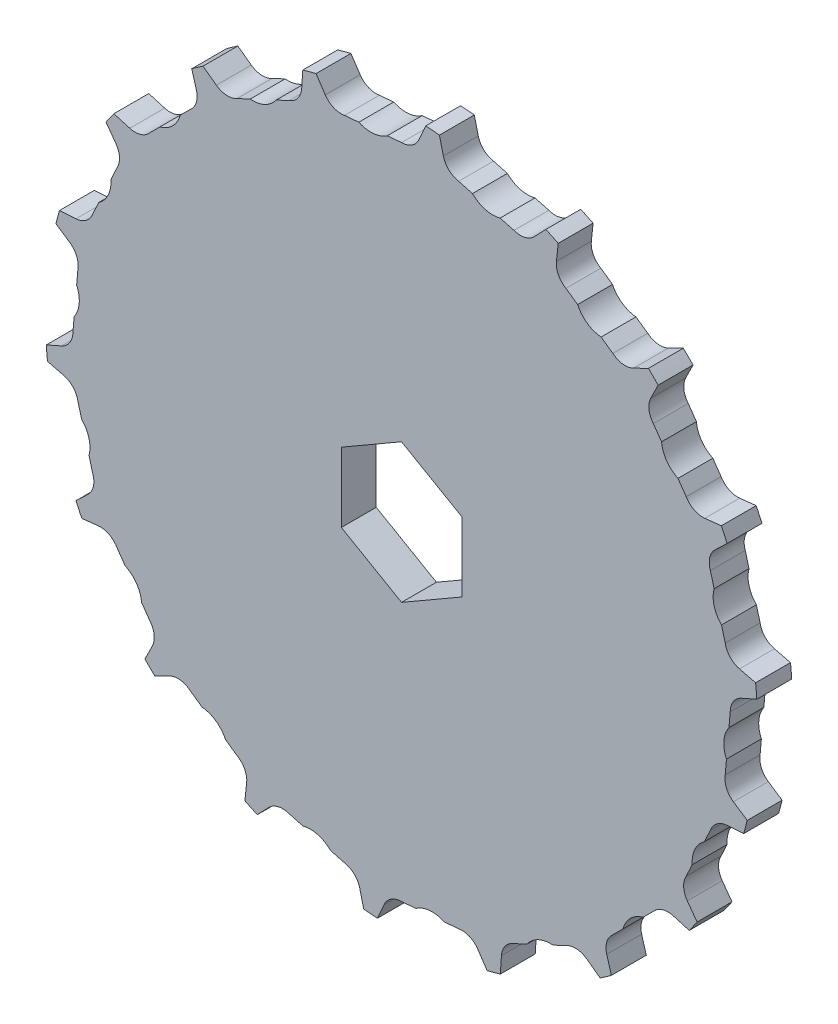
SolidWorks part; units mm, degrees
ref_plane "Front Plane" through (0, 0, 0) normal (0, 0, 1) x (1, 0, 0)
ref_plane "Top Plane" through (0, 0, 0) normal (0, 1, 0) x (1, 0, 0)
ref_plane "Right Plane" through (0, 0, 0) normal (1, 0, 0) x (0, 0, -1)
sketch "Sketch1" plane through (0, 0, 0) normal (0, 0, 1) x (1, 0, 0)
  line L0 (3.6596, 71.1503) -> (5.6741, 75.716)
  line L1 (3.6596, 71.1503) -> (8.7511, 70.7049) construction
  line L2 (7.5601, 75.551) -> (8.7511, 70.7049)
  line L3 (3.6596, 71.1503) -> (0, 0) construction
  line L4 (0, 0) -> (8.7511, 70.7049) construction
  line L5 (15.9591, 69.4339) -> (18.7358, 73.5804)
  line L6 (20.5645, 73.0904) -> (20.8959, 68.1111)
  line L7 (27.7738, 65.6078) -> (31.2283, 69.2091)
  line L8 (32.9441, 68.409) -> (32.4058, 63.4478)
  line L9 (38.7445, 59.7882) -> (42.7719, 62.7349)
  line L10 (44.3227, 61.649) -> (42.9311, 56.8567)
  line L11 (48.538, 52.1519) -> (53.0159, 54.3546)
  line L12 (54.3546, 53.0159) -> (52.1519, 48.538)
  line L13 (56.8567, 42.9311) -> (61.649, 44.3227)
  line L14 (62.7349, 42.7719) -> (59.7882, 38.7445)
  line L15 (63.4478, 32.4058) -> (68.409, 32.9441)
  line L16 (69.2091, 31.2283) -> (65.6078, 27.7738)
  line L17 (68.1111, 20.8959) -> (73.0904, 20.5645)
  line L18 (73.5804, 18.7358) -> (69.4339, 15.9591)
  line L19 (70.7049, 8.7511) -> (75.551, 7.5601)
  line L20 (75.716, 5.6741) -> (71.1503, 3.6596)
  line L21 (71.1503, -3.6596) -> (75.716, -5.6741)
  line L22 (75.551, -7.5601) -> (70.7049, -8.7511)
  line L23 (69.4339, -15.9591) -> (73.5804, -18.7358)
  line L24 (73.0904, -20.5645) -> (68.1111, -20.8959)
  line L25 (65.6078, -27.7738) -> (69.2091, -31.2283)
  line L26 (68.409, -32.9441) -> (63.4478, -32.4058)
  line L27 (59.7882, -38.7445) -> (62.7349, -42.7719)
  line L28 (61.649, -44.3227) -> (56.8567, -42.9311)
  line L29 (52.1519, -48.538) -> (54.3546, -53.0159)
  line L30 (53.0159, -54.3546) -> (48.538, -52.1519)
  line L31 (42.9311, -56.8567) -> (44.3227, -61.649)
  line L32 (42.7719, -62.7349) -> (38.7445, -59.7882)
  line L33 (32.4058, -63.4478) -> (32.9441, -68.409)
  line L34 (31.2283, -69.2091) -> (27.7738, -65.6078)
  line L35 (20.8959, -68.1111) -> (20.5645, -73.0904)
  line L36 (18.7358, -73.5804) -> (15.9591, -69.4339)
  line L37 (8.7511, -70.7049) -> (7.5601, -75.551)
  line L38 (5.6741, -75.716) -> (3.6596, -71.1503)
  line L39 (-3.6596, -71.1503) -> (-5.6741, -75.716)
  line L40 (-7.5601, -75.551) -> (-8.7511, -70.7049)
  line L41 (-15.9591, -69.4339) -> (-18.7358, -73.5804)
  line L42 (-20.5645, -73.0904) -> (-20.8959, -68.1111)
  line L43 (-27.7738, -65.6078) -> (-31.2283, -69.2091)
  line L44 (-32.9441, -68.409) -> (-32.4058, -63.4478)
  line L45 (-38.7445, -59.7882) -> (-42.7719, -62.7349)
  line L46 (-44.3227, -61.649) -> (-42.9311, -56.8567)
  line L47 (-48.538, -52.1519) -> (-53.0159, -54.3546)
  line L48 (-54.3546, -53.0159) -> (-52.1519, -48.538)
  line L49 (-56.8567, -42.9311) -> (-61.649, -44.3227)
  line L50 (-62.7349, -42.7719) -> (-59.7882, -38.7445)
  line L51 (-63.4478, -32.4058) -> (-68.409, -32.9441)
  line L52 (-69.2091, -31.2283) -> (-65.6078, -27.7738)
  line L53 (-68.1111, -20.8959) -> (-73.0904, -20.5645)
  line L54 (-73.5804, -18.7358) -> (-69.4339, -15.9591)
  line L55 (-70.7049, -8.7511) -> (-75.551, -7.5601)
  line L56 (-75.716, -5.6741) -> (-71.1503, -3.6596)
  line L57 (-71.1503, 3.6596) -> (-75.716, 5.6741)
  line L58 (-75.551, 7.5601) -> (-70.7049, 8.7511)
  line L59 (-69.4339, 15.9591) -> (-73.5804, 18.7358)
  line L60 (-73.0904, 20.5645) -> (-68.1111, 20.8959)
  line L61 (-65.6078, 27.7738) -> (-69.2091, 31.2283)
  line L62 (-68.409, 32.9441) -> (-63.4478, 32.4058)
  line L63 (-59.7882, 38.7445) -> (-62.7349, 42.7719)
  line L64 (-61.649, 44.3227) -> (-56.8567, 42.9311)
  line L65 (-52.1519, 48.538) -> (-54.3546, 53.0159)
  line L66 (-53.0159, 54.3546) -> (-48.538, 52.1519)
  line L67 (-42.9311, 56.8567) -> (-44.3227, 61.649)
  line L68 (-42.7719, 62.7349) -> (-38.7445, 59.7882)
  line L69 (-32.4058, 63.4478) -> (-32.9441, 68.409)
  line L70 (-31.2283, 69.2091) -> (-27.7738, 65.6078)
  line L71 (-20.8959, 68.1111) -> (-20.5645, 73.0904)
  line L72 (-18.7358, 73.5804) -> (-15.9591, 69.4339)
  line L73 (-8.7511, 70.7049) -> (-7.5601, 75.551)
  line L74 (-5.6741, 75.716) -> (-3.6596, 71.1503)
  line L83 (0, 72.765) -> (0, 0) construction
  line L84 (0, 0) -> (6.589, 75.3123) construction
  circle A0 centre (0, 0) radius 72.765 construction
  arc A1 (-3.9985, 72.6551) -> (3.6596, 71.1503) centre (0, 72.765) ccw
  arc A2 (4.3155, 72.6369) -> (8.3633, 72.2828) centre (0, 0) cw
  arc A3 (5.6741, 75.716) -> (7.5601, 75.551) centre (6.589, 75.3123) cw
  arc A4 (8.6787, 72.2456) -> (15.9591, 69.4339) centre (12.6355, 71.6595) ccw
  arc A5 (18.7358, 73.5804) -> (20.5645, 73.0904) centre (19.5667, 73.024) cw
  arc A6 (21.0921, 69.641) -> (27.7738, 65.6078) centre (24.8871, 68.3767) ccw
  arc A7 (31.2283, 69.2091) -> (32.9441, 68.409) centre (31.9499, 68.5169) cw
  arc A8 (32.8647, 64.9204) -> (38.7445, 59.7882) centre (36.3825, 63.0163) ccw
  arc A9 (42.7719, 62.7349) -> (44.3227, 61.649) centre (43.3624, 61.9279) cw
  arc A10 (43.6388, 58.2272) -> (48.538, 52.1519) centre (46.7724, 55.7412) ccw
  arc A11 (53.0159, 54.3546) -> (54.3546, 53.0159) centre (53.4573, 53.4573) cw
  arc A12 (53.0868, 49.7648) -> (56.8567, 42.9311) centre (55.7412, 46.7724) ccw
  arc A13 (61.649, 44.3227) -> (62.7349, 42.7719) centre (61.9279, 43.3624) cw
  arc A14 (60.9219, 39.7903) -> (63.4478, 32.4058) centre (63.0163, 36.3825) ccw
  arc A15 (68.409, 32.9441) -> (69.2091, 31.2283) centre (68.5169, 31.9499) cw
  arc A16 (66.9059, 28.6068) -> (68.1111, 20.8959) centre (68.3767, 24.8871) ccw
  arc A17 (73.0904, 20.5645) -> (73.5804, 18.7358) centre (73.024, 19.5667) cw
  arc A18 (70.8569, 16.5542) -> (70.7049, 8.7511) centre (71.6595, 12.6355) ccw
  arc A19 (75.551, 7.5601) -> (75.716, 5.6741) centre (75.3123, 6.589) cw
  arc A20 (72.6551, 3.9985) -> (71.1503, -3.6596) centre (72.765, 0) ccw
  arc A21 (75.716, -5.6741) -> (75.551, -7.5601) centre (75.3123, -6.589) cw
  arc A22 (72.2456, -8.6787) -> (69.4339, -15.9591) centre (71.6595, -12.6355) ccw
  arc A23 (73.5804, -18.7358) -> (73.0904, -20.5645) centre (73.024, -19.5667) cw
  arc A24 (69.641, -21.0921) -> (65.6078, -27.7738) centre (68.3767, -24.8871) ccw
  arc A25 (69.2091, -31.2283) -> (68.409, -32.9441) centre (68.5169, -31.9499) cw
  arc A26 (64.9204, -32.8647) -> (59.7882, -38.7445) centre (63.0163, -36.3825) ccw
  arc A27 (62.7349, -42.7719) -> (61.649, -44.3227) centre (61.9279, -43.3624) cw
  arc A28 (58.2272, -43.6388) -> (52.1519, -48.538) centre (55.7412, -46.7724) ccw
  arc A29 (54.3546, -53.0159) -> (53.0159, -54.3546) centre (53.4573, -53.4573) cw
  arc A30 (49.7648, -53.0868) -> (42.9311, -56.8567) centre (46.7724, -55.7412) ccw
  arc A31 (44.3227, -61.649) -> (42.7719, -62.7349) centre (43.3624, -61.9279) cw
  arc A32 (39.7903, -60.9219) -> (32.4058, -63.4478) centre (36.3825, -63.0163) ccw
  arc A33 (32.9441, -68.409) -> (31.2283, -69.2091) centre (31.9499, -68.5169) cw
  arc A34 (28.6068, -66.9059) -> (20.8959, -68.1111) centre (24.8871, -68.3767) ccw
  arc A35 (20.5645, -73.0904) -> (18.7358, -73.5804) centre (19.5667, -73.024) cw
  arc A36 (16.5542, -70.8569) -> (8.7511, -70.7049) centre (12.6355, -71.6595) ccw
  arc A37 (7.5601, -75.551) -> (5.6741, -75.716) centre (6.589, -75.3123) cw
  arc A38 (3.9985, -72.6551) -> (-3.6596, -71.1503) centre (0, -72.765) ccw
  arc A39 (-5.6741, -75.716) -> (-7.5601, -75.551) centre (-6.589, -75.3123) cw
  arc A40 (-8.6787, -72.2456) -> (-15.9591, -69.4339) centre (-12.6355, -71.6595) ccw
  arc A41 (-18.7358, -73.5804) -> (-20.5645, -73.0904) centre (-19.5667, -73.024) cw
  arc A42 (-21.0921, -69.641) -> (-27.7738, -65.6078) centre (-24.8871, -68.3767) ccw
  arc A43 (-31.2283, -69.2091) -> (-32.9441, -68.409) centre (-31.9499, -68.5169) cw
  arc A44 (-32.8647, -64.9204) -> (-38.7445, -59.7882) centre (-36.3825, -63.0163) ccw
  arc A45 (-42.7719, -62.7349) -> (-44.3227, -61.649) centre (-43.3624, -61.9279) cw
  arc A46 (-43.6388, -58.2272) -> (-48.538, -52.1519) centre (-46.7724, -55.7412) ccw
  arc A47 (-53.0159, -54.3546) -> (-54.3546, -53.0159) centre (-53.4573, -53.4573) cw
  arc A48 (-53.0868, -49.7648) -> (-56.8567, -42.9311) centre (-55.7412, -46.7724) ccw
  arc A49 (-61.649, -44.3227) -> (-62.7349, -42.7719) centre (-61.9279, -43.3624) cw
  arc A50 (-60.9219, -39.7903) -> (-63.4478, -32.4058) centre (-63.0163, -36.3825) ccw
  arc A51 (-68.409, -32.9441) -> (-69.2091, -31.2283) centre (-68.5169, -31.9499) cw
  arc A52 (-66.9059, -28.6068) -> (-68.1111, -20.8959) centre (-68.3767, -24.8871) ccw
  arc A53 (-73.0904, -20.5645) -> (-73.5804, -18.7358) centre (-73.024, -19.5667) cw
  arc A54 (-70.8569, -16.5542) -> (-70.7049, -8.7511) centre (-71.6595, -12.6355) ccw
  arc A55 (-75.551, -7.5601) -> (-75.716, -5.6741) centre (-75.3123, -6.589) cw
  arc A56 (-72.6551, -3.9985) -> (-71.1503, 3.6596) centre (-72.765, 0) ccw
  arc A57 (-75.716, 5.6741) -> (-75.551, 7.5601) centre (-75.3123, 6.589) cw
  arc A58 (-72.2456, 8.6787) -> (-69.4339, 15.9591) centre (-71.6595, 12.6355) ccw
  arc A59 (-73.5804, 18.7358) -> (-73.0904, 20.5645) centre (-73.024, 19.5667) cw
  arc A60 (-69.641, 21.0921) -> (-65.6078, 27.7738) centre (-68.3767, 24.8871) ccw
  arc A61 (-69.2091, 31.2283) -> (-68.409, 32.9441) centre (-68.5169, 31.9499) cw
  arc A62 (-64.9204, 32.8647) -> (-59.7882, 38.7445) centre (-63.0163, 36.3825) ccw
  arc A63 (-62.7349, 42.7719) -> (-61.649, 44.3227) centre (-61.9279, 43.3624) cw
  arc A64 (-58.2272, 43.6388) -> (-52.1519, 48.538) centre (-55.7412, 46.7724) ccw
  arc A65 (-54.3546, 53.0159) -> (-53.0159, 54.3546) centre (-53.4573, 53.4573) cw
  arc A66 (-49.7648, 53.0868) -> (-42.9311, 56.8567) centre (-46.7724, 55.7412) ccw
  arc A67 (-44.3227, 61.649) -> (-42.7719, 62.7349) centre (-43.3624, 61.9279) cw
  arc A68 (-39.7903, 60.9219) -> (-32.4058, 63.4478) centre (-36.3825, 63.0163) ccw
  arc A69 (-32.9441, 68.409) -> (-31.2283, 69.2091) centre (-31.9499, 68.5169) cw
  arc A70 (-28.6068, 66.9059) -> (-20.8959, 68.1111) centre (-24.8871, 68.3767) ccw
  arc A71 (-20.5645, 73.0904) -> (-18.7358, 73.5804) centre (-19.5667, 73.024) cw
  arc A72 (-16.5542, 70.8569) -> (-8.7511, 70.7049) centre (-12.6355, 71.6595) ccw
  arc A73 (-7.5601, 75.551) -> (-5.6741, 75.716) centre (-6.589, 75.3123) cw
  point P13 (3.8108, 71.6595)
  point P289 (0, 0)
  dimension "D1" = 145.53
  dimension "D2" = 4
  dimension "D5" = 1
  dimension "D6" = 75.6
  dimension "D3" = 5
  dimension "D4" = 36
extrude "Boss-Extrude1" add sketch "Sketch1" along normal blind 7.3
sketch "Sketch2" plane through (0, 0, 7.3) normal (0, 0, 1) x (1, 0, 0)
  circle A0 centre (0, 0) radius 12.5
  dimension "D1" = 25
extrude "Boss-Extrude2" add sketch "Sketch2" along normal blind 40
sketch "Sketch5" plane through (0, 0, 0) normal (0, 0, -1) x (-1, 0, 0)
  line L0 (0, 68.765) -> (2.9886, 68.5035)
  line L1 (0, 68.765) -> (0.7057, 76.8309)
  line L2 (11.9409, 67.7203) -> (12.6466, 75.7862)
  line L3 (0.7057, 76.8309) -> (12.6466, 75.7862)
  line L4 (8.9523, 67.9818) -> (11.9409, 67.7203)
  arc A0 (2.9886, 68.5035) -> (8.9523, 67.9818) centre (6.4237, 73.4229) ccw
  arc A3 (-3.6596, 71.1503) -> (3.6596, 71.1503) centre (0, 72.765) ccw construction
  arc A5 (-3.6596, 71.1503) -> (3.6596, 71.1503) centre (0, 72.765) ccw construction
  arc A7 (8.7511, 70.7049) -> (15.9591, 69.4339) centre (12.6355, 71.6595) ccw construction
  arc A8 (7.5601, 75.551) -> (5.6741, 75.716) centre (6.589, 75.3123) ccw construction
  point P8 (0, 0)
  point P9 (0, 0)
  point P12 (0, 0)
  point P19 (0, 68.765)
  point P21 (13.9304, 70.1592)
  point P22 (11.9409, 67.7203)
  dimension "D2" = 3
  dimension "D3" = 3
  dimension "D4" = 6
extrude "Cut-Extrude2" cut sketch "Sketch5" against normal blind 10
sketch "Sketch9" plane through (0, 0, 0) normal (0, 0, -1) x (-1, 0, 0)
  circle A0 centre (0, 0) radius 74.5
  circle A1 centre (0, 0) radius 100
  dimension "D1" = 149
  dimension "D2" = 200
extrude "Cut-Extrude5" cut sketch "Sketch9" against normal blind 10
fillet "Fillet1" radius 30 1 edges at (12.5, 0, 7.3)
sketch "Sketch3" plane through (0, 0, 47.3) normal (0, 0, 1) x (1, 0, 0)
  circle A0 centre (0, 0) radius 5
  dimension "D1" = 10
extrude "Cut-Extrude1" cut sketch "Sketch3" against normal through all
hole_wizard "Ø1.0mm Dowel Hole1" positions "3DSketch1" profile "Sketch4" hole size "Ø1.0" standard "ANSI Metric"
sketch3d "3DSketch1"
  point P0 (-6.8176, -10.4771, 42.0201)
  point P2 (-11.0684, 5.8086, 41.6583)
sketch "Sketch4" plane through (-6.8176, -10.4771, 42.0201) normal (0, 0, 1) x (0.8382, -0.5454, 0)
  line L0 (0, 0) -> (0, 34)
  line L1 (0, 34) -> (1.4, 33.1588)
  line L2 (1.4, 33.1588) -> (1.4, 0)
  line L5 (1.4, 0) -> (0, 0)
  line L10 (0, 34) -> (-1.4, 33.1588) construction
  line L11 (0, -6.35) -> (0, 107.95) construction
  dimension "Hole Dia." = 2.8
  dimension "Hole Depth" = 34
  dimension "Drill Angle" = 118
pattern_circular "CirPattern1" count 18 over 360 about axis through (0, 0, 0) along (0, 0, 1) of "Cut-Extrude2"
sketch "Sketch6" plane through (0, 0, 0) normal (0, 1, 0) x (1, 0, 0)
  line L1 (-74.3279, -7.3) -> (79.9055, -7.3)
  line L2 (-74.3279, -7.3) -> (-74.3279, -52.0573)
  line L3 (-74.3279, -52.0573) -> (79.9055, -52.0573)
  line L4 (79.9055, -7.3) -> (79.9055, -52.0573)
  point P6 (0, 0)
extrude "Cut-Extrude3" cut sketch "Sketch6" against normal through all both and the other way through all
sketch "Sketch7" plane through (0, 0, 0) normal (0, 0, -1) x (-1, 0, 0)
  line L1 (12.6, -7.2746) -> (12.6, 7.2746)
  line L2 (12.6, 7.2746) -> (0, 14.5492)
  line L3 (0, 14.5492) -> (-12.6, 7.2746)
  line L4 (-12.6, 7.2746) -> (-12.6, -7.2746)
  line L5 (-12.6, -7.2746) -> (0, -14.5492)
  line L6 (0, -14.5492) -> (12.6, -7.2746)
  circle A0 centre (0, 0) radius 12.6 construction
  dimension "D1" = 25.2
extrude "Cut-Extrude4" cut sketch "Sketch7" against normal through all both
sketch "Sketch8" plane through (0, 0, 7.3) normal (0, 0, 1) x (1, 0, 0)
  circle A0 centre (-12.6355, 71.6595) radius 12.7
  circle A1 centre (-12.6355, 71.6595) radius 8.7313
  circle A2 centre (-24.9213, 68.4425) radius 3.9687
  circle A5 centre (-24.9213, 68.4425) radius 12.7
  circle A6 centre (-34.2074, 77.1061) radius 3.9687
  point P9 (-0.9221, 76.5673)
  point P10 (-37.5946, 66.9475)
  point P12 (-36.4464, 62.9279)
  point P13 (-22.3387, 79.8534)
  point P14 (-36.7901, 79.5156)
  point P15 (-24.9213, 68.4425)
  dimension "D1" = 25.4
  dimension "D2" = 17.4625
  dimension "D3" = 7.9375
  dimension "D4" = 25.4
  dimension "D5" = 7.9375
equation "\"Teeth\" = 36"
equation "\"D4@Sketch1\"=\"Teeth\""
equation "\"D6@Sketch1\"=84/40*\"Teeth\""
equation "\"D1@Sketch1\"=161.70/40*\"Teeth\""
equation "\"D3@Sketch1\"=4.5/\"Teeth\"*40"
equation "\"D1@CirPattern1\"=\"Teeth\"/2"
